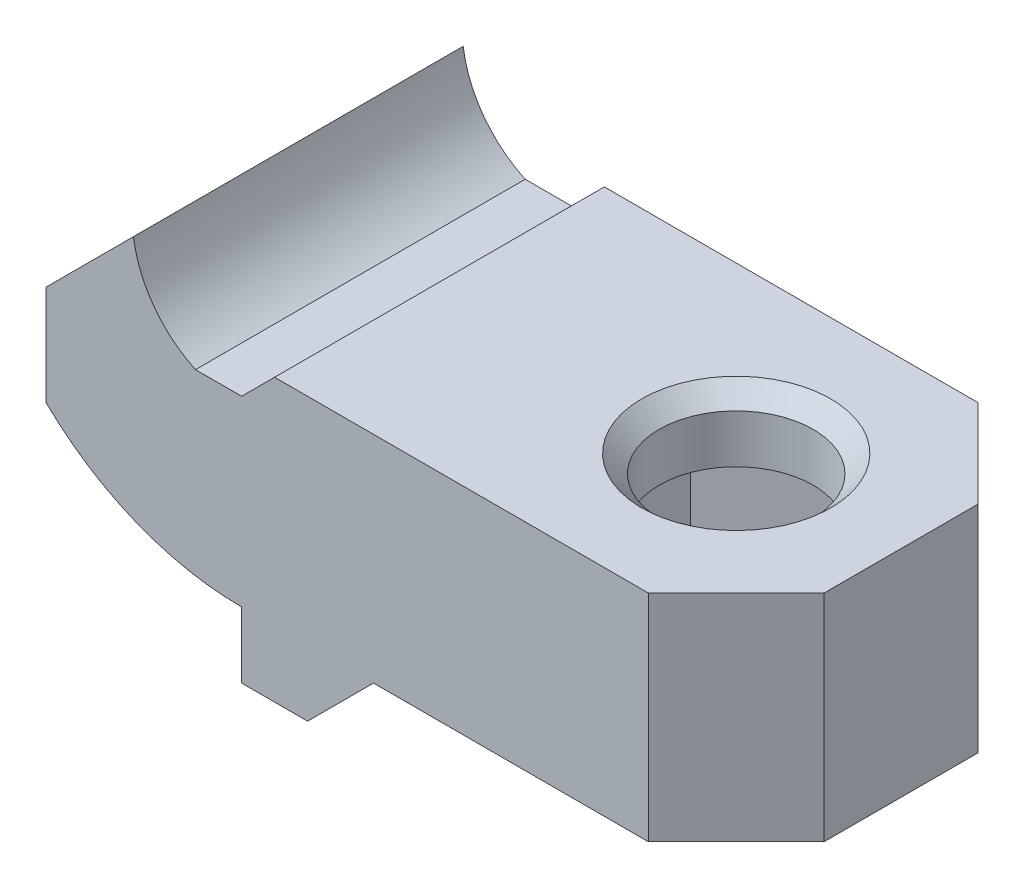
SolidWorks part; units mm, degrees
ref_plane "Alzado" through (0, 0, 0) normal (0, 0, 1) x (1, 0, 0)
ref_plane "Planta" through (0, 0, 0) normal (0, 1, 0) x (1, 0, 0)
ref_plane "Vista lateral" through (0, 0, 0) normal (1, 0, 0) x (0, 0, -1)
sketch "Croquis1" plane through (0, 0, 0) normal (0, 0, 1) x (1, 0, 0)
  line L0 (0, 0) -> (0, 5301.9663) construction
  line L1 (0, 0) -> (5301.9663, 0) construction
  line L2 (-4.8553, 4.15) -> (5297.111, 4.15) construction
  line L3 (0, 4.15) -> (-2.1, 4.15) construction
  line L4 (-8.9, 5.9678) -> (-8.9, -5295.9985) construction
  line L5 (-2.1, 7.8714) -> (-2.1, -5294.095) construction
  line L6 (-2.1, 4.15) -> (-2.1, 8.4) construction
  line L8 (-8.9, 4) -> (-8.9, -4) construction
  line L10 (-2.1, -4.15) -> (-2.1, -8.4) construction
  line L11 (0, -4.15) -> (-2.1, -4.15) construction
  line L12 (0, 4.15) -> (0, -4.15) construction
  line L13 (-4.5, -15.5102) -> (-4.5, 49984.4898) construction
  line L14 (-2.1, -8.4) -> (-4.5, -8.4) construction
  line L15 (-4.5, -8.4) -> (-8.9, -4) construction
  line L16 (-4.5, 8.4) -> (-8.9, 4) construction
  line L17 (-2.1, 8.4) -> (-4.5, 8.4) construction
  line L18 (17.5111, 5.65) -> (-49982.4889, 5.65) construction
  line L19 (23.2911, 8.65) -> (-49976.7089, 8.65) construction
  line L20 (-8.9, 4) -> (-4.9204, 7.9796)
  line L22 (-8.9, 4) -> (-8.9, -0.5495)
  line L23 (-2.1, 4.15) -> (0, 4.15)
  line L24 (0, 4.15) -> (0, -4.15)
  circle A0 centre (0, 8.65) radius 4.9659 construction
  circle A1 centre (0, 8.65) radius 12.8 construction
  arc A4 (0, -4.15) -> (-8.9, -0.5495) centre (0, 8.65) cw
  arc A5 (-2.1, 4.15) -> (-4.9204, 7.9796) centre (0, 8.65) cw
  point P17 (-8.9, 0)
  dimension "D1" = 8
  dimension "D2" = 6.8
  dimension "D3" = 2.1
  dimension "D4" = 8.3
  dimension "D5" = 16.8
  dimension "D6" = 2.4
  dimension "D7" = 1.5
  dimension "D8" = 3
extrude "Saliente-Extruir1" add sketch "Croquis1" along normal mid plane 15
sketch "Croquis6" plane through (0, 0, -7.5) normal (0, 0, -1) x (-1, 0, 0)
  line L0 (0, 0) -> (-50000, 0) construction
  line L1 (0, 0) -> (0, 50000) construction
  line L2 (-15, 0) -> (-15, 50000) construction
  line L3 (-3.8361, 5.65) -> (-50003.8361, 5.65) construction
  line L4 (0, -4.15) -> (0, -7.15)
  line L5 (0, 4.15) -> (-1.5, 5.65)
  line L6 (-1.5, 5.65) -> (-22.5, 5.65)
  line L7 (-22.5, 5.65) -> (-22.5, -4.15)
  line L8 (-22.5, -4.15) -> (0, -4.15) construction
  line L9 (0, -4.15) -> (0, 4.15)
  line L10 (0, 4.15) -> (2.1, 4.15) construction
  line L11 (0, -7.15) -> (-3, -7.15)
  line L12 (-3, -7.15) -> (-6, -4.15)
  line L13 (-6, -4.15) -> (-22.5, -4.15)
  arc A0 (0, -4.15) -> (8.9, -0.5495) centre (0, 8.65) ccw construction
  dimension "D1" = 15
  dimension "D2" = 1.5
  dimension "D3" = 15
  dimension "D4" = 45
  dimension "D5" = 3
  dimension "D6" = 3
  dimension "D7" = 45
extrude "Saliente-Extruir2" add sketch "Croquis6" against normal through all
sketch "Croquis7" plane through (0, 5.65, 0) normal (0, 1, 0) x (1, 0, 0)
  line L0 (0, 0) -> (50000, 0) construction
  line L1 (15, 0) -> (15, 50000) construction
  circle A0 centre (15, 0) radius 3.5
  dimension "D2" = 7
  dimension "D1" = 15
extrude "Cortar-Extruir4" cut sketch "Croquis7" against normal through all
sketch "Croquis8" plane through (0, 5.65, 0) normal (0, 1, 0) x (1, 0, 0)
  line L1 (15, 5.658) -> (10.1, 2.829)
  line L2 (10.1, 2.829) -> (10.1, -2.829)
  line L3 (10.1, -2.829) -> (15, -5.658)
  line L4 (15, -5.658) -> (19.9, -2.829)
  line L5 (19.9, -2.829) -> (19.9, 2.829)
  line L6 (19.9, 2.829) -> (15, 5.658)
  circle A0 centre (15, 0) radius 4.9 construction
  dimension "D1" = 9.8
extrude "Cortar-Extruir5" cut sketch "Croquis8" against normal blind 10 from offset 3 offset against normal yes
chamfer "Chaflán4" distance 4 angle 45 2 edges at (22.5, 0.75, -7.5) (22.5, 0.75, 7.5)
chamfer "Chaflán5" distance 0.8 angle 45 7 edges at (10.1, -4.15, 0) (12.55, -4.15, 4.2435) (17.45, -4.15, 4.2435) (19.9, -4.15, 0) (17.45, -4.15, -4.2435) (12.55, -4.15, -4.2435) (11.5, 5.65, 0)
